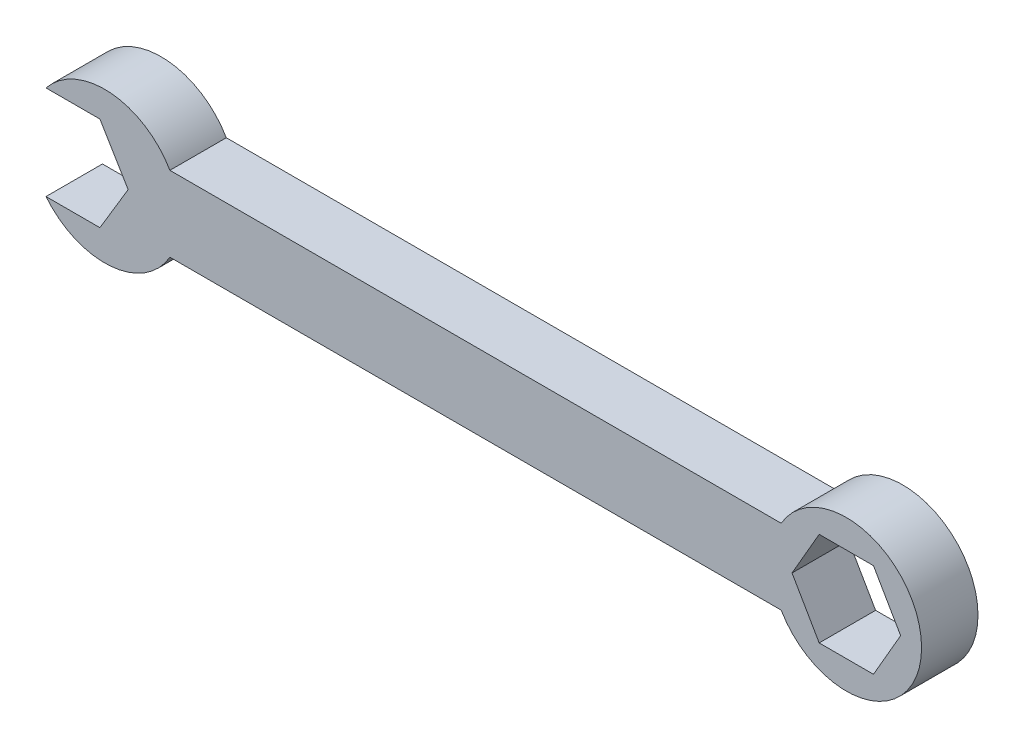
SolidWorks part; units mm, degrees
ref_plane "Front Plane" through (0, 0, 0) normal (0, 0, 1) x (1, 0, 0)
ref_plane "Top Plane" through (0, 0, 0) normal (0, 1, 0) x (1, 0, 0)
ref_plane "Right Plane" through (0, 0, 0) normal (1, 0, 0) x (0, 0, -1)
sketch "Sketch1" plane through (0, 0, 0) normal (0, 0, 1) x (1, 0, 0)
  line L0 (0.4033, 0) -> (0, 0)
  line L1 (-58.005, 6.35) -> (-50.7239, 6.35)
  line L2 (-41.275, 5.08) -> (41.275, 5.08)
  line L4 (-41.275, -5.08) -> (41.275, -5.08)
  line L6 (-41.275, 5.08) -> (41.275, -5.08) construction
  line L7 (-41.275, -5.08) -> (41.275, 5.08) construction
  line L8 (57.4062, 0) -> (53.74, 6.35)
  line L9 (53.74, 6.35) -> (46.4076, 6.35)
  line L10 (46.4076, 6.35) -> (42.7415, 0)
  line L11 (42.7415, 0) -> (46.4076, -6.35)
  line L12 (46.4076, -6.35) -> (53.74, -6.35)
  line L13 (53.74, -6.35) -> (57.4062, 0)
  line L14 (-58.005, -6.35) -> (-50.7239, -6.35)
  line L19 (-46.9139, 0) -> (-50.7239, -6.35)
  line L20 (-50.7239, 6.35) -> (-46.9139, 0)
  arc A0 (41.275, -5.08) -> (41.275, 5.08) centre (50.0738, 0) ccw
  arc A1 (-58.005, -6.35) -> (-41.275, -5.08) centre (-50.0738, 0) ccw
  circle A2 centre (50.0738, 0) radius 6.35 construction
  arc A3 (-41.275, 5.08) -> (-58.005, 6.35) centre (-50.0738, 0) ccw
  point P10 (0, 0)
  point P22 (-54.3644, -6.35)
  dimension "D3" = 20.32
  dimension "D4" = 20.32
  dimension "D1" = 82.55
  dimension "D2" = 10.16
  dimension "D5" = 12.7
  dimension "D6" = 6.35
  dimension "D7" = 6.35
extrude "Boss-Extrude1" add sketch "Sketch1" along normal blind 7.62
